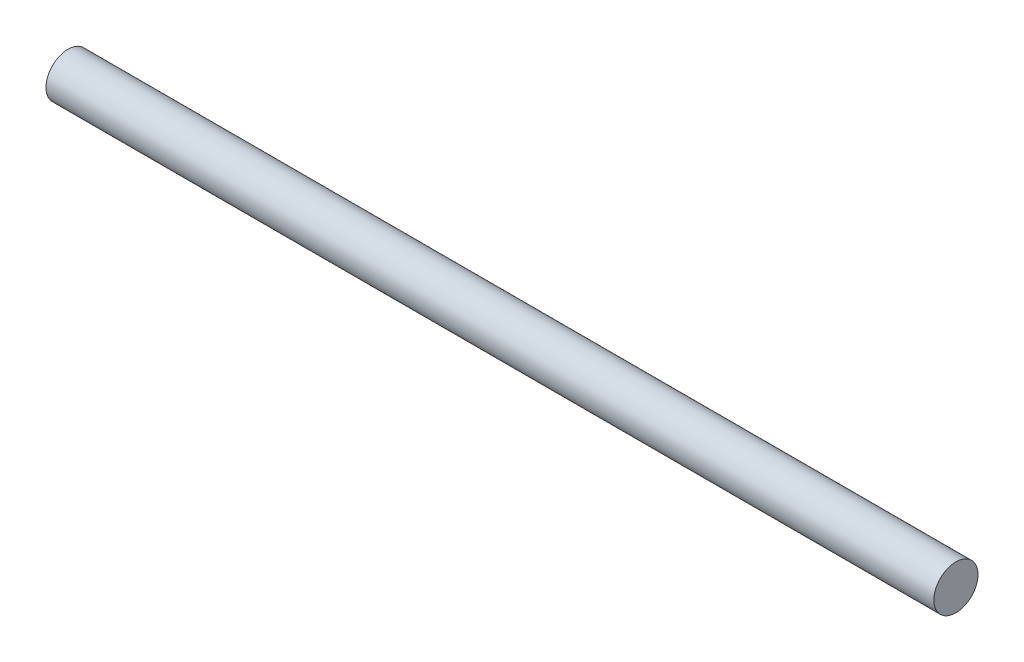
SolidWorks part; units mm, degrees
material "Thornel Mat VMA"
ref_plane "Front Plane" through (0, 0, 0) normal (0, 0, 1) x (1, 0, 0)
ref_plane "Top Plane" through (0, 0, 0) normal (0, 1, 0) x (1, 0, 0)
ref_plane "Right Plane" through (0, 0, 0) normal (1, 0, 0) x (0, 0, -1)
sketch "Sketch3" plane through (0, 0, 0) normal (1, 0, 0) x (0, 0, -1)
  circle A0 centre (0, 0) radius 1.5
  dimension "D1" = 3
extrude "Boss-Extrude1" add sketch "Sketch3" along normal mid plane 60.3
